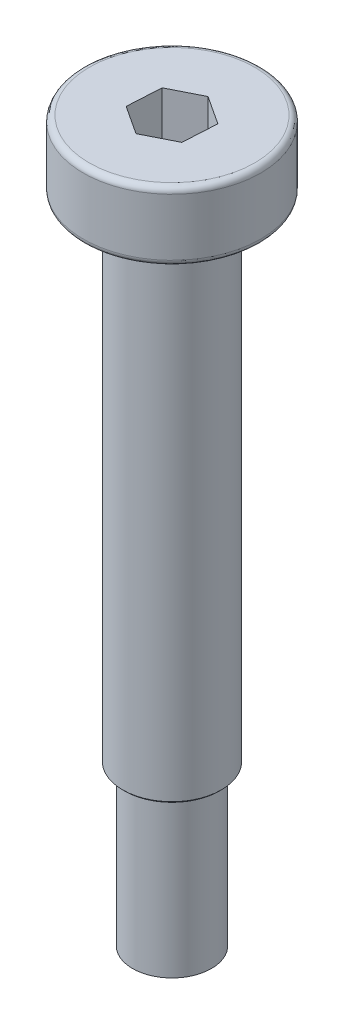
SolidWorks part; units mm, degrees
ref_plane "前视基准面" through (0, 0, 0) normal (0, 0, 1) x (1, 0, 0)
ref_plane "上视基准面" through (0, 0, 0) normal (0, 1, 0) x (1, 0, 0)
ref_plane "右视基准面" through (0, 0, 0) normal (1, 0, 0) x (0, 0, -1)
sketch "草图1" plane through (0, 0, 0) normal (0, 0, 1) x (1, 0, 0)
  line L0 (0, 0) -> (-4.5, 0)
  line L1 (-4.5, 0) -> (-4.5, -3.5)
  line L2 (-4.5, -3.5) -> (-2.5, -3.5)
  line L3 (-2.5, -3.5) -> (-2.5, -28.5)
  line L4 (-2.5, -28.5) -> (-2, -28.5)
  line L5 (-2, -28.5) -> (-2, -36.5)
  line L6 (-2, -36.5) -> (0, -36.5)
  line L7 (0, -36.5) -> (0, 0) construction
  line L8 (0, 0) -> (0, -36.5)
  dimension "D1" = 4.5
  dimension "D2" = 2
  dimension "D3" = 8
  dimension "D4" = 25
  dimension "D5" = 3.5
  dimension "D6" = 2.5
revolve "旋转1" add sketch "草图1" angle 360 about L7
cosmetic thread "装饰螺纹线1" parameters "D2"=3
fillet "圆角2" radius 0.3 2 edges at (4.5, -3.5, 0) (4.5, 0, 0)
sketch "草图2" plane through (0, 0, 0) normal (0, 1, 0) x (1, 0, 0)
  line L1 (1.4487, -0.9493) -> (1.5465, 0.78)
  line L2 (1.5465, 0.78) -> (0.0978, 1.7293)
  line L3 (0.0978, 1.7293) -> (-1.4487, 0.9493)
  line L4 (-1.4487, 0.9493) -> (-1.5465, -0.78)
  line L5 (-1.5465, -0.78) -> (-0.0978, -1.7293)
  line L6 (-0.0978, -1.7293) -> (1.4487, -0.9493)
  circle A0 centre (0, 0) radius 1.5 construction
  dimension "D1" = 3
extrude "切除-拉伸1" cut sketch "草图2" against normal blind 2.4
chamfer "倒角2" distance 0.1 angle 45 1 edges at (2.5, -28.5, 0)
